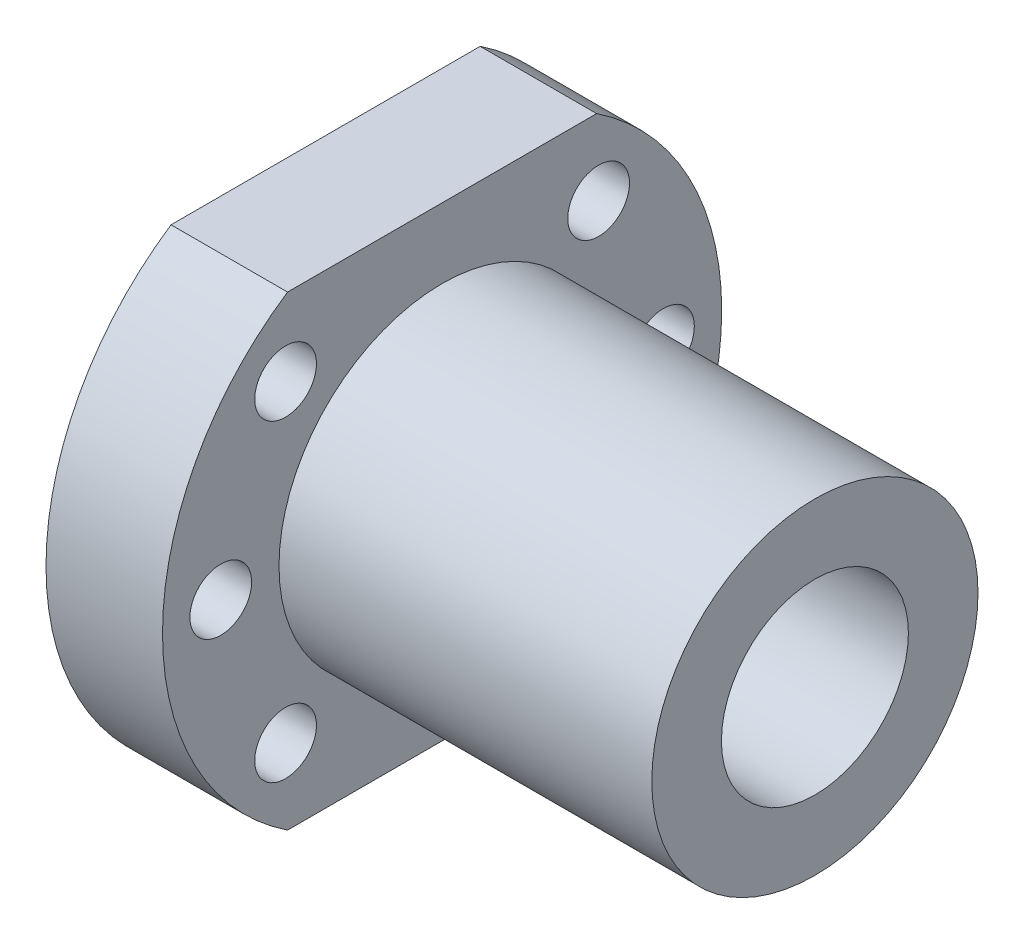
SolidWorks part; units mm, degrees
ref_plane "Front Plane" through (0, 0, 0) normal (0, 0, 1) x (1, 0, 0)
ref_plane "Top Plane" through (0, 0, 0) normal (0, 1, 0) x (1, 0, 0)
ref_plane "Right Plane" through (0, 0, 0) normal (1, 0, 0) x (0, 0, -1)
ref_plane "Plane1" through (0, 0, 0) normal (-1, 0, 0) x (0, -1, 0)
sketch "Sketch1" plane through (0, 0, 0) normal (-1, 0, 0) x (0, -1, 0)
  line L0 (20, -13.2665) -> (20, 13.2665)
  line L1 (-20, 13.2665) -> (-20, -13.2665)
  arc A0 (-20, -13.2665) -> (20, -13.2665) centre (0, 0) ccw
  arc A1 (20, 13.2665) -> (-20, 13.2665) centre (0, 0) ccw
extrude "Boss-Extrude1" add sketch "Sketch1" against normal blind 10
sketch "Sketch2" plane through (0, 0, 0) normal (0, 0, 1) x (1, 0, 0)
  line L0 (10, 14) -> (10, 0)
  line L1 (10, 0) -> (42, 0)
  line L2 (42, 0) -> (42, 14)
  line L3 (42, 14) -> (10, 14)
  line L4 (10, 0) -> (42, 0) construction
revolve "Revolve1" add sketch "Sketch2" angle 360 about L4
hole_wizard "Hole1" positions "Sketch4" profile "Sketch3" legacy
sketch "Sketch4" plane through (42, 0, 0) normal (1, 0, 0) x (0, 0, -1)
  point P0 (0, 0)
sketch "Sketch3" plane through (42, 0, 0) normal (0, 1, 0) x (0, 0, -1)
  line L0 (0, 0) -> (0, 42)
  line L1 (0, 42) -> (8.025, 42)
  line L2 (8.025, 42) -> (8.025, 0)
  line L3 (8.025, 0) -> (0, 0)
  line L4 (0, 110) -> (0, -10) construction
  dimension "Diameter" = 16.05
  dimension "Depth" = 42
hole_wizard "M5 Clearance Hole1" positions "Sketch6" profile "Sketch5" hole size "M5" standard "ANSI Metric" end condition through all
sketch "Sketch6" plane through (10, 0, 0) normal (1, 0, 0) x (0, 0, -1)
  line L1 (0, 0) -> (-13.435, -13.435) construction
  line L4 (0, 0) -> (-24, 0) construction
  arc A0 (-13.2665, 20) -> (-13.2665, -20) centre (0, 0) ccw construction
  point P5 (-13.435, -13.435)
  point P23 (0, 0)
  point P24 (0, 0)
  point P25 (0, 0)
  point P26 (0, 0)
  point P27 (0, 0)
  dimension "D1" = 19
  dimension "D2" = 45
sketch "Sketch5" plane through (10, -13.435, 13.435) normal (0, 1, 0) x (0, 0, -1)
  line L0 (0, 0) -> (0, 10)
  line L1 (0, 10) -> (2.65, 10)
  line L2 (2.65, 10) -> (2.65, 0)
  line L5 (2.65, 0) -> (0, 0)
  line L11 (0, -6.35) -> (0, 107.95) construction
  dimension "Thru Hole Dia." = 5.3
  dimension "Thru Hole Depth" = 10
pattern_circular "CirPattern1" count 3 every 45 about axis through (0, 0, 0) along (1, 0, 0) of "M5 Clearance Hole1"
mirror "Mirror1" about plane through (0, 0, 0) normal (0, 0, 1) of "CirPattern1", "M5 Clearance Hole1"
